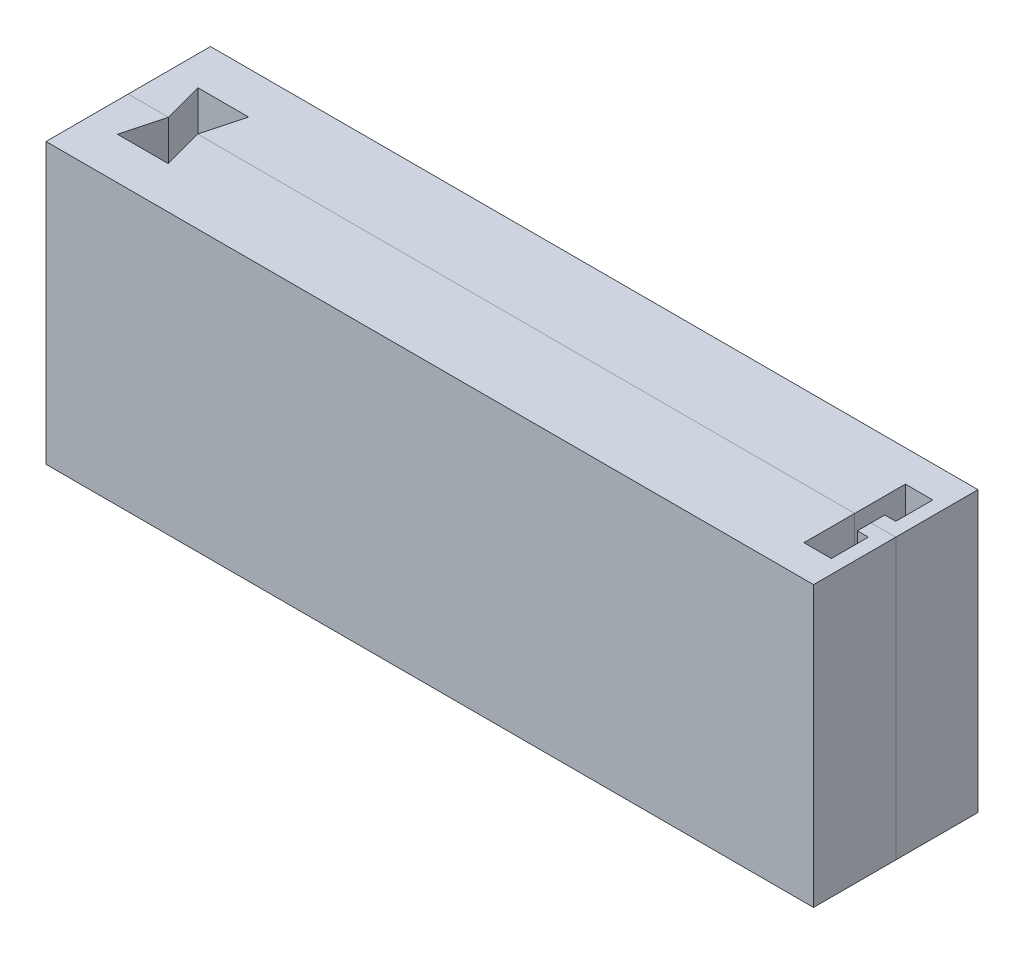
SolidWorks part; units mm, degrees
ref_plane "Front Plane" through (0, 0, 0) normal (0, 0, 1) x (1, 0, 0)
ref_plane "Top Plane" through (0, 0, 0) normal (0, 1, 0) x (1, 0, 0)
ref_plane "Right Plane" through (0, 0, 0) normal (1, 0, 0) x (0, 0, -1)
sketch "Sketch1" plane through (0, 0, 0) normal (0, 0, 1) x (1, 0, 0)
  line L1 (-60.9366, 28.6127) -> (79.0634, 28.6127)
  line L2 (-60.9366, 28.6127) -> (-60.9366, -22.3873)
  line L3 (-60.9366, -22.3873) -> (79.0634, -22.3873)
  line L4 (79.0634, 28.6127) -> (79.0634, -22.3873)
  dimension "D1" = 51
  dimension "D2" = 140
extrude "Boss-Extrude1" add sketch "Sketch1" along normal blind 15
sketch "Sketch2" plane through (0, 28.6127, 0) normal (0, 1, 0) x (1, 0, 0)
  line L0 (79.0634, 0) -> (74.5634, 0)
  line L6 (79.0634, 0) -> (-60.9366, 0) construction
  line L7 (74.5634, 0) -> (71.5634, 0)
  line L8 (71.5634, 0) -> (71.5634, -2.5)
  line L9 (71.5634, -2.5) -> (71.5634, -9.25)
  line L10 (71.5634, -9.25) -> (76.5634, -9.25)
  line L11 (74.5634, 0) -> (74.5634, -2.5)
  line L12 (74.5634, -2.5) -> (76.5634, -2.5)
  line L13 (76.5634, -2.5) -> (76.5634, -9.25)
  line M13 (79.0634, 0) -> (-60.9366, 0)
  dimension "D1" = 4.5
  dimension "D2" = 3
  dimension "D3" = 2.5
  dimension "D4" = 6.75
  dimension "D5" = 5
extrude "Cut-Extrude1" cut sketch "Sketch2" against normal through all contours L13 L12 L11 L8 L9 L10 M13
sketch "Sketch3" plane through (0, 28.6127, 0) normal (0, 1, 0) x (1, 0, 0)
  line L0 (-60.9366, 0) -> (-53.5866, 0)
  line L2 (71.5634, 0) -> (-60.9366, 0) construction
  line L3 (-53.5866, 0) -> (-55.5536, -7.341)
  line L4 (-55.5536, -7.341) -> (-46.3196, -7.341)
  line L5 (-46.3196, -7.341) -> (-48.2866, 0)
  dimension "D1" = 7.35
  dimension "D2" = 105
  dimension "D3" = 105
  dimension "D4" = 75
  dimension "D5" = 75
  dimension "D6" = 7.6
  dimension "D7" = 7.6
  dimension "D8" = 5.3
  dimension "D9" = 9.234
extrude "Cut-Extrude2" cut sketch "Sketch3" against normal blind 26 and the other way through all
mirror "Mirror1" about plane through (0, 0, 0) normal (0, 0, 1) of bodies 103
